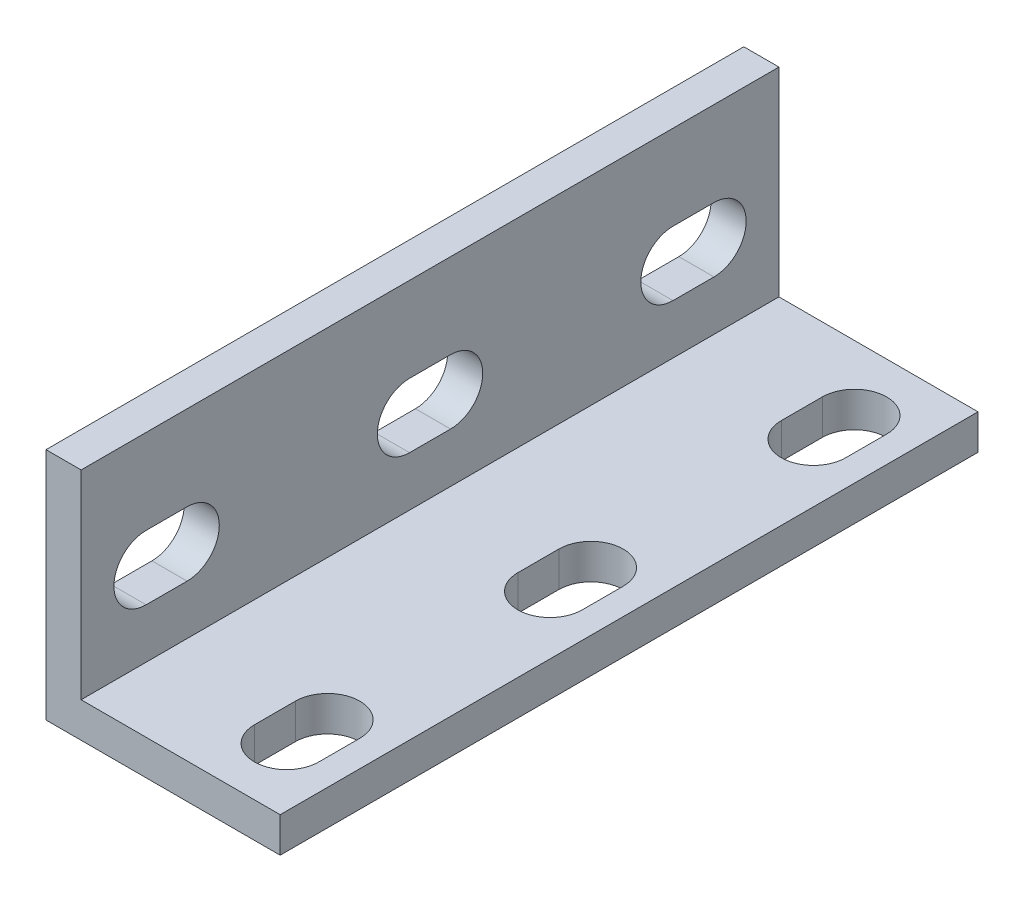
SolidWorks part; units mm, degrees
material "6061-T6 (SS)"
ref_plane "Front Plane" through (0, 0, 0) normal (0, 0, 1) x (1, 0, 0)
ref_plane "Top Plane" through (0, 0, 0) normal (0, 1, 0) x (1, 0, 0)
ref_plane "Right Plane" through (0, 0, 0) normal (1, 0, 0) x (0, 0, -1)
sketch "Sketch1" plane through (0, 0, 0) normal (0, 0, 1) x (1, 0, 0)
  line L0 (0, 20) -> (0, 0)
  line L1 (0, 0) -> (20, 0)
  dimension "D1" = 20
extrude "Extrude-Thin1" add sketch "Sketch1" along normal blind 59.6 thin thin type one direction reverse wall 3
sketch "Sketch2" plane through (3, 0, 0) normal (1, 0, 0) x (0, 0, -1)
  line L0 (-29.8, 20) -> (-29.8, 3) construction
  line L1 (-59.6, 20) -> (0, 20) construction
  line L2 (-59.6, 3) -> (0, 3) construction
  line L3 (-50.55, 10) -> (-54.05, 10) construction
  line L4 (-50.55, 7.25) -> (-54.05, 7.25)
  line L5 (-50.55, 12.75) -> (-54.05, 12.75)
  line L6 (-9.05, 10) -> (-5.55, 10) construction
  line L7 (-9.05, 7.25) -> (-5.55, 7.25)
  line L8 (-59.6, 3) -> (0, 3) construction
  line L9 (-9.05, 12.75) -> (-5.55, 12.75)
  line L10 (-28.05, 10) -> (-31.55, 10) construction
  line L11 (-28.05, 7.25) -> (-31.55, 7.25)
  line L12 (-28.05, 12.75) -> (-31.55, 12.75)
  arc A0 (-50.55, 7.25) -> (-50.55, 12.75) centre (-50.55, 10) ccw
  arc A1 (-54.05, 12.75) -> (-54.05, 7.25) centre (-54.05, 10) ccw
  arc A2 (-9.05, 7.25) -> (-9.05, 12.75) centre (-9.05, 10) cw
  arc A3 (-5.55, 12.75) -> (-5.55, 7.25) centre (-5.55, 10) cw
  arc A4 (-28.05, 7.25) -> (-28.05, 12.75) centre (-28.05, 10) ccw
  arc A5 (-31.55, 12.75) -> (-31.55, 7.25) centre (-31.55, 10) ccw
  point P8 (-52.3, 10)
  point P15 (-7.3, 10)
  point P24 (-29.8, 10)
  dimension "D1" = 3.5
  dimension "D2" = 5.5
  dimension "D3" = 7
  dimension "D4" = 45
extrude "Cut-Extrude1" cut sketch "Sketch2" against normal through all
sketch "Sketch3" plane through (0, 3, 0) normal (0, 1, 0) x (1, 0, 0)
  line L0 (20, -29.8) -> (3, -29.8) construction
  line L1 (20, -59.6) -> (20, 0) construction
  line L2 (3, -59.6) -> (3, 0) construction
  line L3 (15, -54.05) -> (15, -50.55) construction
  line L4 (12.25, -54.05) -> (12.25, -50.55)
  line L5 (17.75, -54.05) -> (17.75, -50.55)
  line L6 (15, -5.55) -> (15, -9.05) construction
  line L7 (12.25, -5.55) -> (12.25, -9.05)
  line L8 (17.75, -5.55) -> (17.75, -9.05)
  line L9 (15, -28.05) -> (15, -31.55) construction
  line L10 (17.75, -28.05) -> (17.75, -31.55)
  line L11 (12.25, -28.05) -> (12.25, -31.55)
  arc A0 (12.25, -54.05) -> (17.75, -54.05) centre (15, -54.05) ccw
  arc A1 (17.75, -50.55) -> (12.25, -50.55) centre (15, -50.55) ccw
  arc A2 (12.25, -5.55) -> (17.75, -5.55) centre (15, -5.55) cw
  arc A3 (17.75, -9.05) -> (12.25, -9.05) centre (15, -9.05) cw
  arc A4 (17.75, -28.05) -> (12.25, -28.05) centre (15, -28.05) ccw
  arc A5 (12.25, -31.55) -> (17.75, -31.55) centre (15, -31.55) ccw
  point P8 (15, -52.3)
  point P15 (15, -7.3)
  point P22 (15, -29.8)
  dimension "D1" = 3.5
  dimension "D2" = 5.5
  dimension "D3" = 12
  dimension "D4" = 45
extrude "Cut-Extrude2" cut sketch "Sketch3" against normal through all
